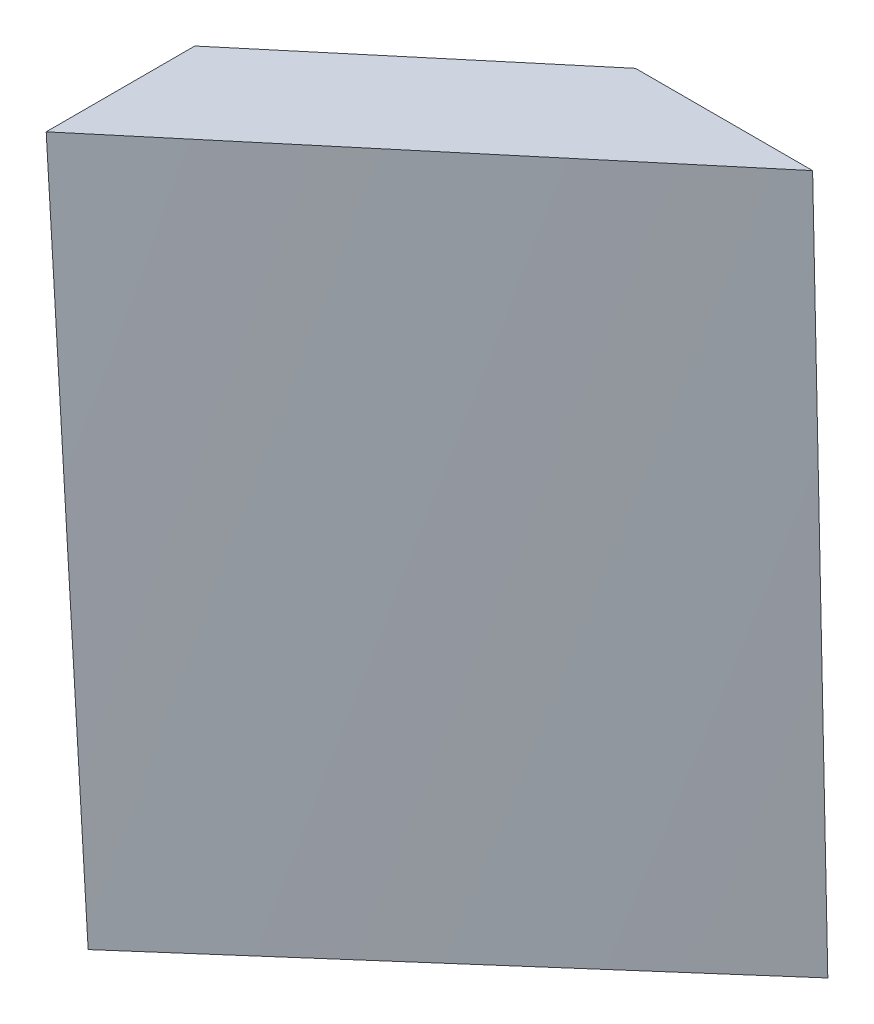
SolidWorks part; units mm, degrees
ref_plane "Alzado" through (0, 0, 0) normal (0, 0, 1) x (1, 0, 0)
ref_plane "Planta" through (0, 0, 0) normal (0, 1, 0) x (1, 0, 0)
ref_plane "Vista lateral" through (0, 0, 0) normal (1, 0, 0) x (0, 0, -1)
sketch "Croquis1" plane through (0, 0, 0) normal (0, 1, 0) x (1, 0, 0)
  line L0 (0, 0) -> (0, 16.32)
  line L1 (0, 16.32) -> (23.8637, 37.9088)
  line L2 (23.8637, 37.9088) -> (43.3137, 37.9088)
  line L3 (43.3137, 37.9088) -> (0, 0)
  dimension "D1" = 57.56
  dimension "D2" = 19.45
  dimension "D3" = 16.32
  dimension "D4" = 32.18
ref_plane "Plano1" through (0, 75, 0) normal (0, 1, 0) x (1, 0, 0)
sketch "Croquis2" plane through (0, 75, 0) normal (0, 1, 0) x (1, 0, 0)
  line L0 (40.6939, 38.8588) -> (21.2437, 38.8588)
  line L1 (21.2437, 38.8588) -> (-5.0756, 16.7859)
  line L2 (-5.0756, 16.7859) -> (-5.0756, 0.4659)
  line L3 (-5.0756, 0.4659) -> (40.6939, 38.8588)
  line L4 (23.8637, 37.9088) -> (21.2437, 37.9088) construction
  line L5 (21.2437, 37.9088) -> (21.2437, 38.8588) construction
  point P2 (0, 0)
  point P7 (0, 0)
  point P8 (-2.559, 14.0929)
  point P11 (-1.5444, 41.257)
  point P12 (-17.2638, 40.4759)
  point P13 (-14.519, 45.2432)
  point P14 (-44.7045, 52.4007)
  point P15 (-47.413, 48.9269)
  point P16 (0, 0)
  dimension "D1" = 34.35
  dimension "D2" = 2.62
  dimension "D3" = 0.95
  dimension "D4" = 59.74
  dimension "D5" = 16.32
  dimension "D6" = 12.5
loft "Recubrir1" add profiles "Croquis2", "Croquis1"
